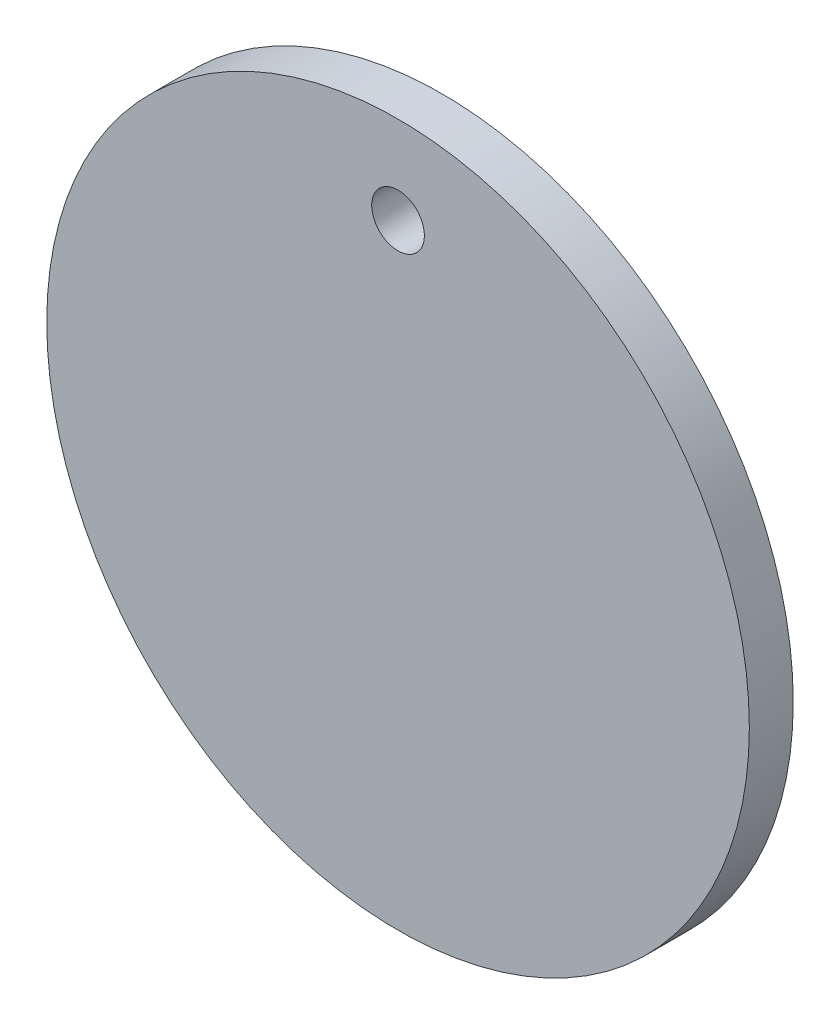
SolidWorks part; units mm, degrees
ref_plane "Front Plane" through (0, 0, 0) normal (0, 0, 1) x (1, 0, 0)
ref_plane "Top Plane" through (0, 0, 0) normal (0, 1, 0) x (1, 0, 0)
ref_plane "Right Plane" through (0, 0, 0) normal (1, 0, 0) x (0, 0, -1)
sketch "Sketch1" plane through (0, 0, 0) normal (0, 0, 1) x (1, 0, 0)
  circle A0 centre (0, 0) radius 25.4
  circle A1 centre (0, 0) radius 19.05 construction
  circle A2 centre (0, 19.05) radius 1.905
  dimension "D1" = 50.8
  dimension "D2" = 6.35
  dimension "D3" = 3.81
extrude "Boss-Extrude1" add sketch "Sketch1" along normal blind 3.175
